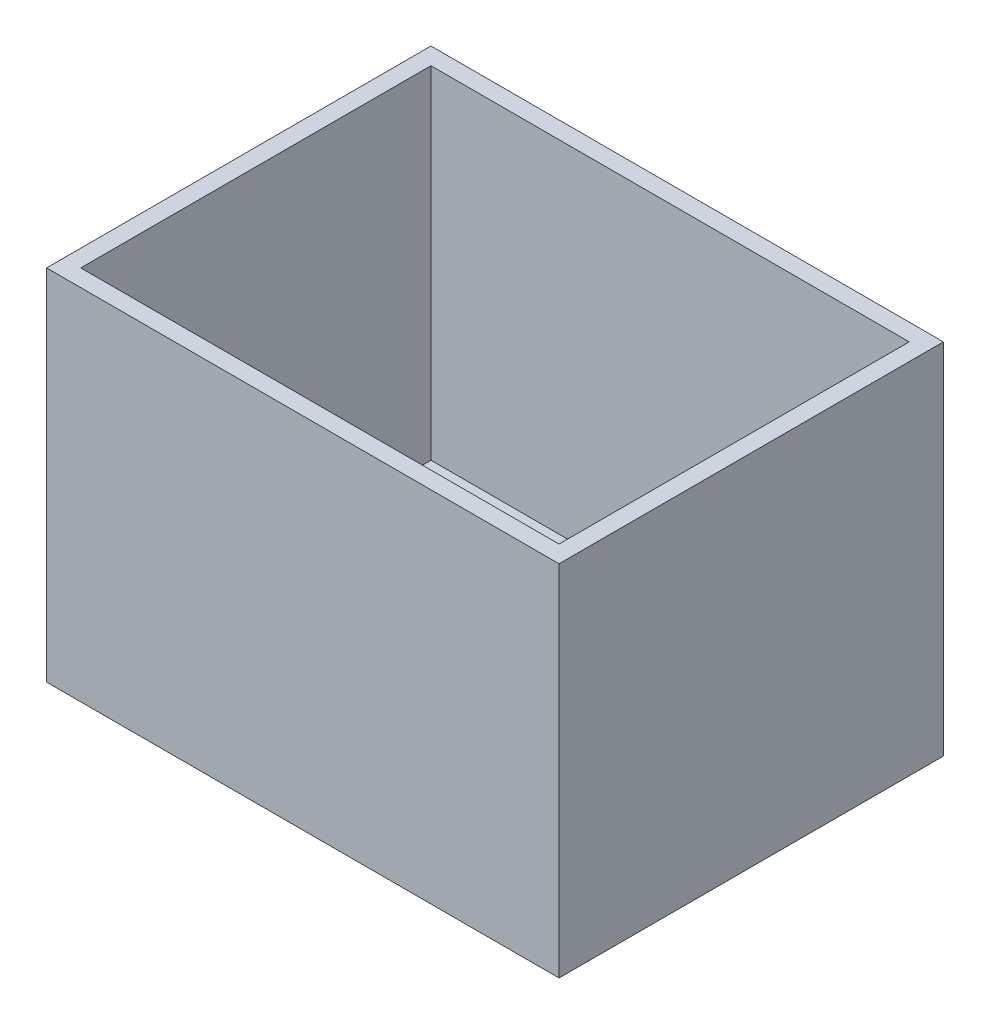
SolidWorks part; units mm, degrees
ref_plane "Front Plane" through (0, 0, 0) normal (0, 0, 1) x (1, 0, 0)
ref_plane "Top Plane" through (0, 0, 0) normal (0, 1, 0) x (1, 0, 0)
ref_plane "Right Plane" through (0, 0, 0) normal (1, 0, 0) x (0, 0, -1)
sketch "Sketch1" plane through (0, 0, 0) normal (0, 1, 0) x (1, 0, 0)
  line L0 (-300, -225) -> (-300, 225)
  line L1 (-280, -205) -> (280, -205)
  line L2 (-280, -205) -> (-280, 205)
  line L3 (-280, 205) -> (280, 205)
  line L4 (280, -205) -> (280, 205)
  line L5 (-280, -205) -> (280, 205) construction
  line L6 (-280, 205) -> (280, -205) construction
  line L7 (-300, 225) -> (300, 225)
  line L8 (300, -225) -> (300, 225)
  line L9 (-300, -225) -> (300, -225)
  point P0 (0, 0)
  dimension "D1" = 560
  dimension "D2" = 410
  dimension "D3" = 20
extrude "Boss-Extrude1" add sketch "Sketch1" along normal blind 400
sketch "Sketch2" plane through (0, 0, 0) normal (0, -1, 0) x (1, 0, 0)
  line L1 (-300, -225) -> (300, -225)
  line L2 (-300, -225) -> (-300, 225)
  line L3 (-300, 225) -> (300, 225)
  line L4 (300, -225) -> (300, 225)
  line L5 (-300, -225) -> (300, 225) construction
  line L6 (-300, 225) -> (300, -225) construction
  point P0 (0, 0)
extrude "Boss-Extrude2" add sketch "Sketch2" along normal blind 20
sketch "Sketch4" plane through (0, 0, 0) normal (0, 1, 0) x (1, 0, 0)
  line L0 (280, 205) -> (-280, 205) construction
  line L1 (-140, 205) -> (-130, 205)
  line L2 (-140, 205) -> (-140, -205)
  line L3 (-140, -205) -> (-130, -205)
  line L4 (-130, 205) -> (-130, -205)
  line L5 (-280, -205) -> (280, -205) construction
  dimension "D1" = 140
  dimension "D2" = 10
extrude "Boss-Extrude4" [suppressed] add sketch "Sketch4" along normal blind 350
sketch "Sketch5" [suppressed] plane through (0, 0, 0) normal (0, 1, 0) x (1, 0, 0)
  line L0 (280, 205) -> (-130, 205) construction
  line L1 (-140, -205) -> (-130, -205)
  line L2 (-140, -205) -> (-140, 205)
  line L3 (-140, 205) -> (-130, 205)
  line L4 (-130, -205) -> (-130, 205)
  line L5 (-130, 205) -> (-140, 205) construction
extrude "Cut-Extrude1" [suppressed] cut sketch "Sketch5" along normal blind 50
